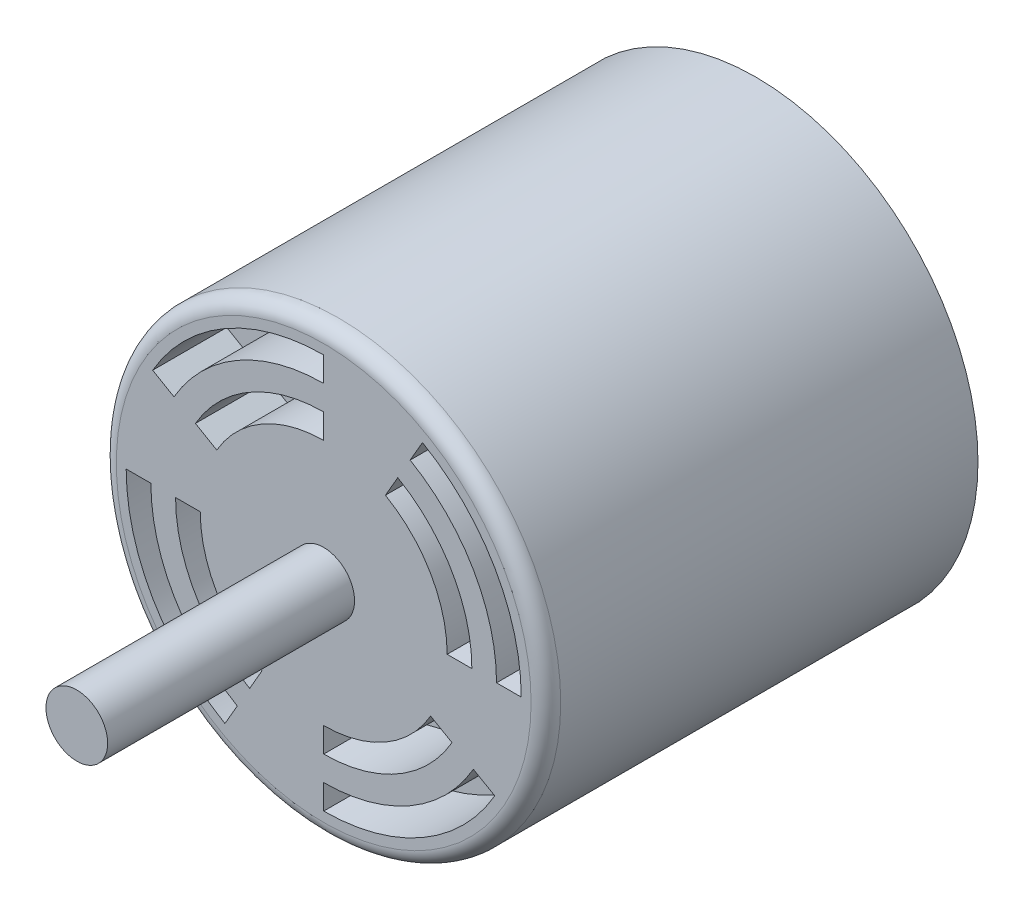
SolidWorks part; units mm, degrees
ref_plane "Ön Düzlem" through (0, 0, 0) normal (0, 0, 1) x (1, 0, 0)
ref_plane "Üst Düzlem" through (0, 0, 0) normal (0, 1, 0) x (1, 0, 0)
ref_plane "Sağ Düzlem" through (0, 0, 0) normal (1, 0, 0) x (0, 0, -1)
sketch "Çizim1" plane through (0, 0, 0) normal (0, 0, 1) x (1, 0, 0)
  circle A0 centre (0, 0) radius 22.86
  dimension "D1" = 45.72
extrude "Yükseklik-Ekstrüzyon1" add sketch "Çizim1" along normal blind 44.45
sketch "Çizim2" plane through (0, 0, 44.45) normal (0, 0, 1) x (1, 0, 0)
  circle A0 centre (0, 0) radius 3.175
  dimension "D1" = 6.35
extrude "Yükseklik-Ekstrüzyon2" add sketch "Çizim2" along normal blind 25.4
sketch "Çizim3" plane through (0, 0, 44.45) normal (0, 0, 1) x (1, 0, 0)
  line L0 (12.7, 0) -> (15.24, 0)
  line L1 (6.35, 10.9985) -> (7.62, 13.1982)
  line L2 (8.89, 15.3979) -> (10.16, 17.5976)
  line L3 (17.78, 0) -> (20.32, 0)
  line L4 (10.9985, -6.35) -> (13.1982, -7.62)
  line L5 (0, -12.7) -> (0, -15.24)
  line L6 (0, -17.78) -> (0, -20.32)
  line L7 (15.3979, -8.89) -> (17.5976, -10.16)
  line L8 (-6.35, -10.9985) -> (-7.62, -13.1982)
  line L9 (-12.7, 0) -> (-15.24, 0)
  line L10 (-17.78, 0) -> (-20.32, 0)
  line L11 (-8.89, -15.3979) -> (-10.16, -17.5976)
  line L12 (-10.9985, 6.35) -> (-13.1982, 7.62)
  line L13 (0, 12.7) -> (0, 15.24)
  line L14 (0, 17.78) -> (0, 20.32)
  line L15 (-15.3979, 8.89) -> (-17.5976, 10.16)
  arc A0 (12.7, 0) -> (6.35, 10.9985) centre (0, 0) ccw
  arc A1 (15.24, 0) -> (7.62, 13.1982) centre (0, 0) ccw
  arc A2 (20.32, 0) -> (10.16, 17.5976) centre (0, 0) ccw
  arc A3 (17.78, 0) -> (8.89, 15.3979) centre (0, 0) ccw
  circle A4 centre (0, 0) radius 20.32 construction
  circle A5 centre (0, 0) radius 17.78 construction
  circle A6 centre (0, 0) radius 15.24 construction
  circle A7 centre (0, 0) radius 12.7 construction
  arc A8 (0, -12.7) -> (10.9985, -6.35) centre (0, 0) ccw
  arc A9 (0, -15.24) -> (13.1982, -7.62) centre (0, 0) ccw
  arc A10 (0, -17.78) -> (15.3979, -8.89) centre (0, 0) ccw
  arc A11 (0, -20.32) -> (17.5976, -10.16) centre (0, 0) ccw
  arc A12 (-12.7, 0) -> (-6.35, -10.9985) centre (0, 0) ccw
  arc A13 (-15.24, 0) -> (-7.62, -13.1982) centre (0, 0) ccw
  arc A14 (-17.78, 0) -> (-8.89, -15.3979) centre (0, 0) ccw
  arc A15 (-20.32, 0) -> (-10.16, -17.5976) centre (0, 0) ccw
  arc A16 (0, 12.7) -> (-10.9985, 6.35) centre (0, 0) ccw
  arc A17 (0, 15.24) -> (-13.1982, 7.62) centre (0, 0) ccw
  arc A18 (0, 17.78) -> (-15.3979, 8.89) centre (0, 0) ccw
  arc A19 (0, 20.32) -> (-17.5976, 10.16) centre (0, 0) ccw
  point P44 (0, 0)
  dimension "D1" = 25.4
  dimension "D5" = 60
  dimension "D2" = 2.54
  dimension "D3" = 7.62
  dimension "D4" = 5.08
  dimension "D6" = 4
extrude "Kes-Ekstrüzyon1" cut sketch "Çizim3" against normal blind 7.62
fillet "Radyus1" radius 1.524 1 edges at (22.86, 0, 44.45)
